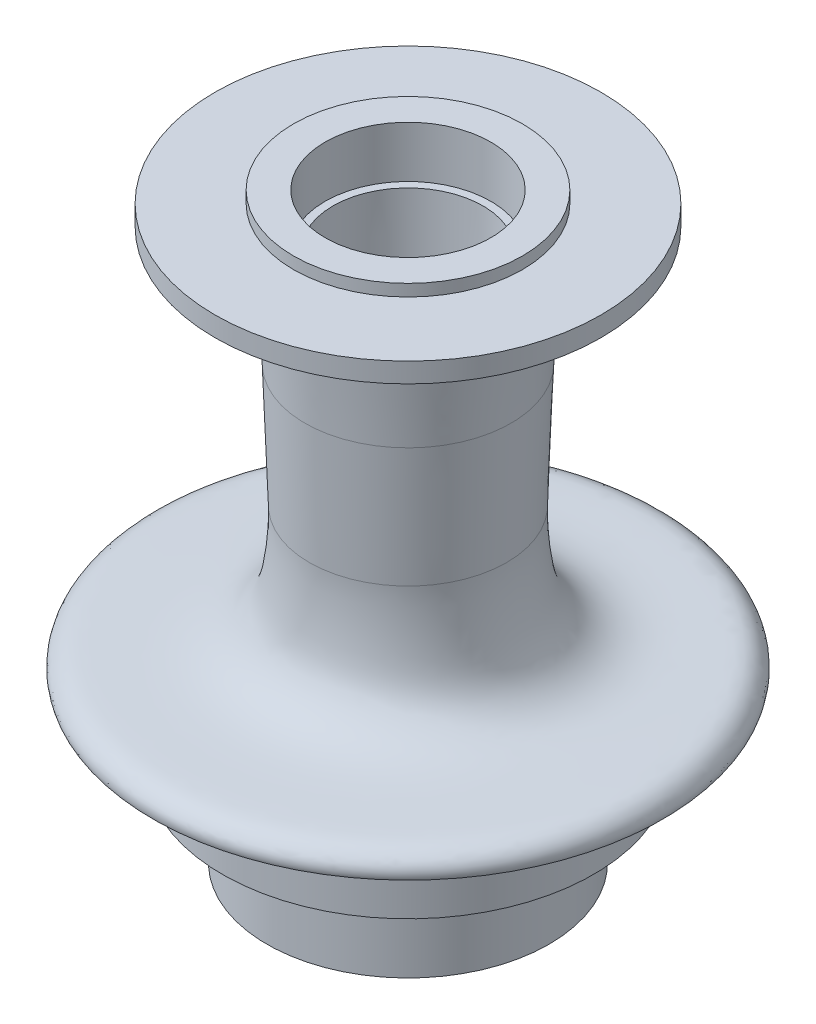
SolidWorks part; units mm, degrees
other "Markup1"
sketch "Sketch2" plane through (-65.2414, 87.7149, -65.2414) normal (-0.2718, 0.6961, -0.6645) x (0.4958, 0.6931, 0.5232)
ref_plane "Front Plane" through (0, 0, 0) normal (0, 0, 1) x (1, 0, 0)
ref_plane "Top Plane" through (0, 0, 0) normal (0, 1, 0) x (1, 0, 0)
ref_plane "Right Plane" through (0, 0, 0) normal (1, 0, 0) x (0, 0, -1)
sketch "Sketch1" plane through (0, 0, 0) normal (0, 0, 1) x (1, 0, 0)
  line L0 (0, 926.0277) -> (0, -1061.2755) construction
  line L1 (19, 74.8173) -> (21, 74.8173)
  line L2 (21, 74.8173) -> (21, 87.8173)
  line L3 (21, 87.8173) -> (0, 87.8173) construction
  line L4 (15.5, -23.4806) -> (17.5, -23.4806)
  line L5 (17.5, -23.4806) -> (17.5, -34.4806)
  line L6 (17.5, -34.4806) -> (0, -34.4806) construction
  line L7 (19, 74.8173) -> (15.5, -23.4806)
  line L8 (21, 87.8173) -> (29, 87.8173)
  line L9 (29, 87.8173) -> (29, 84.8173)
  line L10 (29, 84.8173) -> (48.8849, 84.8173)
  line L11 (48.8849, 84.8173) -> (48.8849, 79.8173)
  line L12 (48.8849, 79.8173) -> (37.2623, 79.8173)
  line L13 (17.5, -34.4806) -> (31.3604, -34.4806)
  line L14 (31.3604, -34.4806) -> (31.3604, -39.3216)
  line L15 (35.75, -59.7999) -> (33.4343, -59.7999)
  line L16 (35.75, -59.7999) -> (35.75, -38.86)
  line L17 (35.75, -38.86) -> (47, -38.86)
  line L18 (47, -38.86) -> (47, -17.987)
  line L19 (33.4343, -59.7999) -> (31.3604, -39.3216)
  line L20 (-139.9834, 1780.2693) -> (1560.0166, 1780.2693) construction
  line L21 (47, -17.987) -> (64.5281, -17.987)
  line L23 (-34.4857, 87.917) -> (44.752, 87.917)
  line L25 (26.1101, 49.682) -> (25.0024, 18.5714)
  spline S0 degree 3 poles (37.2623, 79.8173) (35.3175, 79.8173) (31.5764, 78.9561) (28.5048, 74.723) (26.8115, 69.2251) (27.0234, 67.0118) (26.5294, 61.4574) (26.1101, 49.682) knots 0 0 0 0 0.027814 0.048077 0.056131 0.10835 0.258096 0.258096 0.258096 0.258096
  spline S1 degree 3 poles (64.5281, -17.987) (65.305, -15.791) (62.4956, -12.4033) (55.3788, -12.0374) (46.5053, -12.035) (35.9904, -11.1656) (27.9786, -4.7113) (25.4398, 5.527) (24.8632, 14.6636) (25.0024, 18.5714) knots 0 0 0 0 0.0974 0.161218 0.3246 0.514717 0.634012 0.770814 1 1 1 1
  point P7 (0, 63.2979)
  point P27 (24.4273, -7.6917)
  point P30 (37.2623, 80.0735)
  point P33 (31.3604, 77.8955)
  point P35 (28.1355, 73.4358)
  point P36 (0, 0)
  point P39 (0, 0)
  point P40 (24.5419, 5.5539)
  point P41 (24.9796, 15.1838)
  point P43 (24.5408, 0.8221)
  point P46 (26.8784, -6.567)
  point P48 (25.0334, 1.6103)
  point P50 (28.1355, -5.0892)
  point P52 (24.9349, 4.1718)
  point P54 (33.4343, -9.7197)
  point P55 (24.9868, 18.5719)
  point P56 (26.1101, 3.7756)
  point P57 (29, -4.596)
  point P58 (34.9159, -9.5605)
  point P59 (47, -11.8968)
  dimension "D1" = 21
  dimension "D2" = 17.5
  dimension "D3" = 105.8043
  dimension "D4" = 13
  dimension "D5" = 11
  dimension "D6" = 2
  dimension "D7" = 2
  dimension "D8" = 29
  dimension "D9" = 3
  dimension "D10" = 47
  dimension "D11" = 35.75
  dimension "D12" = 5
  dimension "D13" = 64.5281
  dimension "D14" = 8
revolve "Revolve1" add sketch "Sketch1" angle 360 about L0
sketch "Sketch3" plane through (0, 0, 0) normal (1, 0, 0) x (0, 0, -1)
  line L0 (-35.75, -59.7999) -> (35.75, -59.7999) construction
  line L1 (-32.6673, -59.7999) -> (32.12, -59.7999)
  line L2 (-32.6673, -59.7999) -> (-32.6673, -38.86)
  line L3 (-32.6673, -38.86) -> (32.12, -38.86)
  line L4 (32.12, -59.7999) -> (32.12, -38.86)
  line L5 (-35.75, -38.86) -> (35.75, -38.86) construction
extrude "Boss-Extrude1" add sketch "Sketch3" along normal up to next
